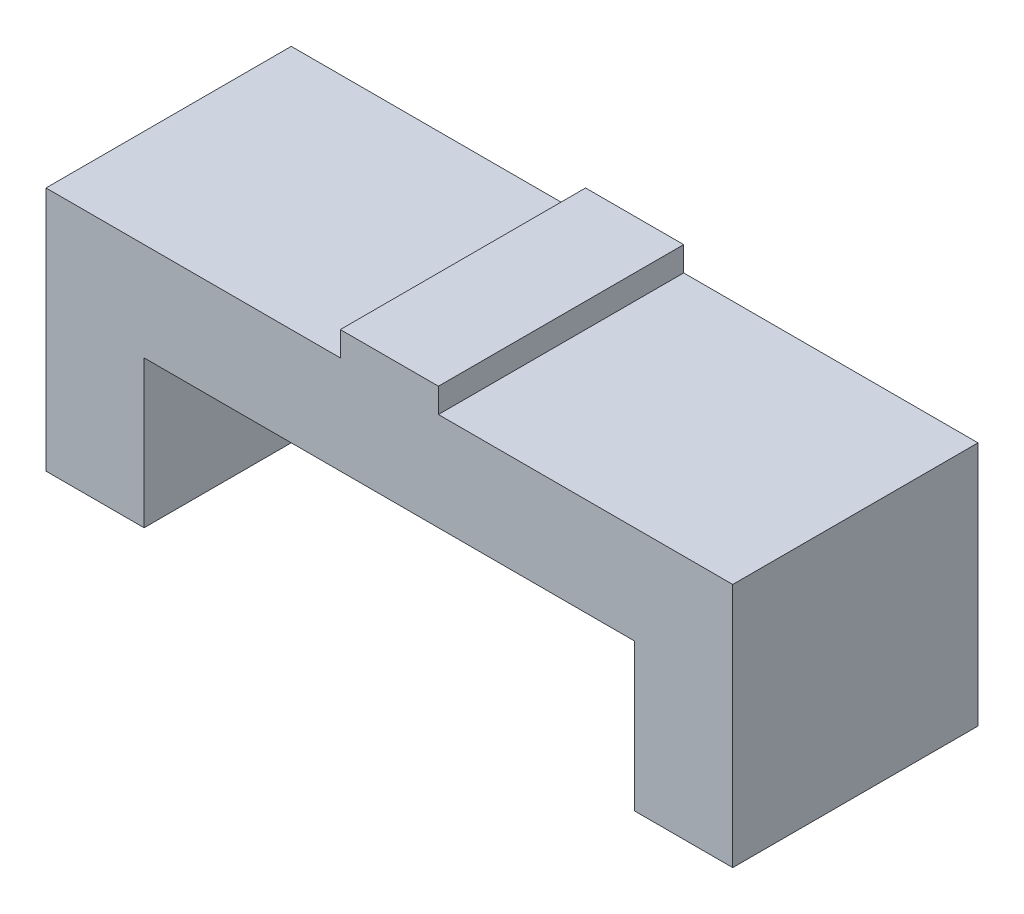
SolidWorks part; units mm, degrees
material "ABS PC"
ref_plane "Front Plane" through (0, 0, 0) normal (0, 0, 1) x (1, 0, 0)
ref_plane "Top Plane" through (0, 0, 0) normal (0, 1, 0) x (1, 0, 0)
ref_plane "Right Plane" through (0, 0, 0) normal (1, 0, 0) x (0, 0, -1)
sketch "Sketch1" plane through (0, 0, 0) normal (0, 0, 1) x (1, 0, 0)
  line L1 (-50, 0) -> (50, 0)
  line L2 (-50, 0) -> (-50, 30)
  line L3 (-50, 30) -> (50, 30)
  line L4 (50, 0) -> (50, 30)
  line L5 (70, 0) -> (-70, 0)
  line L6 (70, 0) -> (70, 50)
  line L7 (70, 50) -> (-70, 50)
  line L8 (-70, 0) -> (-70, 50)
  point P8 (0, 0)
  point P9 (0, 0)
  dimension "D1" = 100
  dimension "D2" = 30
  dimension "D3" = 20
  dimension "D4" = 20
extrude "Boss-Extrude1" add sketch "Sketch1" along normal blind 50 contours L8 L5 L2 L3 L4 L6 L7
sketch "Sketch2" plane through (0, 50, 0) normal (0, 1, 0) x (1, 0, 0)
  line L0 (70, 0) -> (-70, 0) construction
  line L1 (-10, -50) -> (10, -50)
  line L2 (-10, -50) -> (-10, 0)
  line L3 (-10, 0) -> (10, 0)
  line L4 (10, -50) -> (10, 0)
  line L5 (-10, -50) -> (10, 0) construction
  line L6 (-10, 0) -> (10, -50) construction
  line L7 (70, -50) -> (-70, -50) construction
  line L8 (70, -50) -> (70, 0) construction
  point P0 (0, -25)
  dimension "D1" = 70
  dimension "D2" = 20
extrude "Boss-Extrude2" add sketch "Sketch2" along normal blind 5
